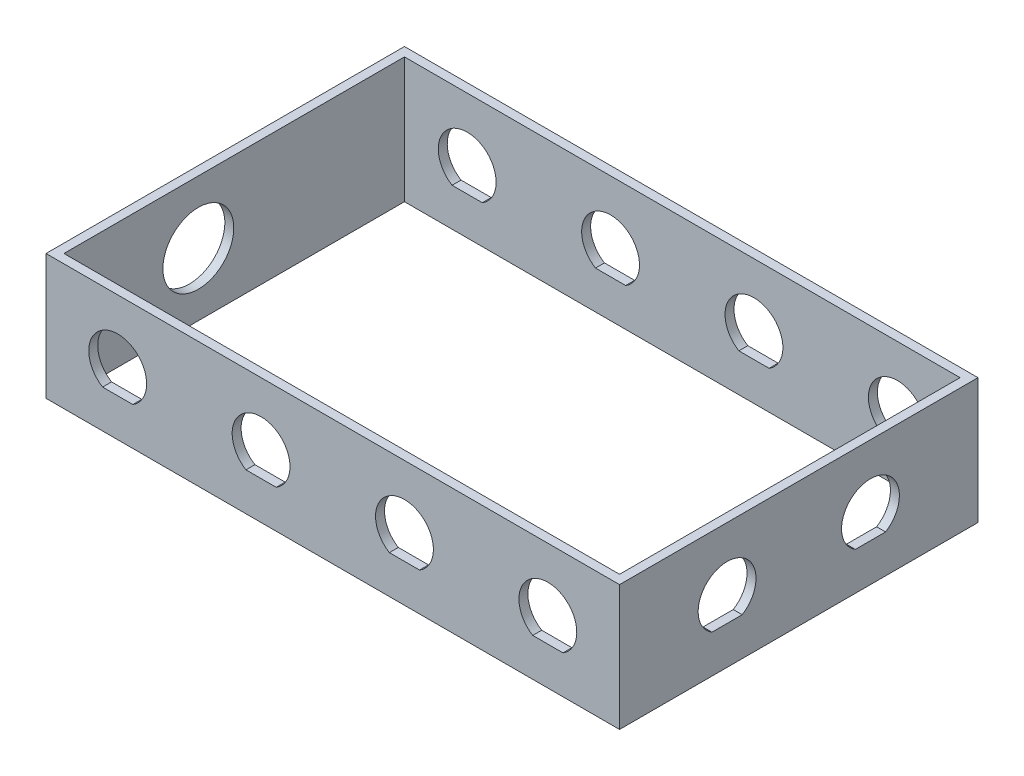
SolidWorks part; units mm, degrees
material "1060 Alloy"
ref_plane "Front Plane" through (0, 0, 0) normal (0, 0, 1) x (1, 0, 0)
ref_plane "Top Plane" through (0, 0, 0) normal (0, 1, 0) x (1, 0, 0)
ref_plane "Right Plane" through (0, 0, 0) normal (1, 0, 0) x (0, 0, -1)
sketch "Sketch1" plane through (0, 0, 0) normal (0, 1, 0) x (1, 0, 0)
  line L1 (101.6, -63.5) -> (-101.6, -63.5)
  line L2 (101.6, -63.5) -> (101.6, 63.5)
  line L3 (101.6, 63.5) -> (-101.6, 63.5)
  line L4 (-101.6, -63.5) -> (-101.6, 63.5)
  line L5 (101.6, -63.5) -> (-101.6, 63.5) construction
  line L6 (101.6, 63.5) -> (-101.6, -63.5) construction
  point P0 (0, 0)
  dimension "D1" = 127
  dimension "D2" = 203.2
extrude "Boss-Extrude1" add sketch "Sketch1" along normal blind 44.45
sketch "Sketch2" plane through (0, 44.45, 0) normal (0, 1, 0) x (1, 0, 0)
  line L8 (-98.425, 60.325) -> (-98.425, -60.325)
  line L9 (98.425, 60.325) -> (-98.425, 60.325)
  line L10 (98.425, -60.325) -> (98.425, 60.325)
  line L11 (-98.425, -60.325) -> (98.425, -60.325)
  line L12 (-98.425, 60.325) -> (-98.425, -60.325)
  line L13 (98.425, 60.325) -> (-98.425, 60.325)
  line L14 (98.425, -60.325) -> (98.425, 60.325)
  line L15 (-98.425, -60.325) -> (98.425, -60.325)
  dimension "D1" = 3.175
extrude "Cut-Extrude1" cut sketch "Sketch2" against normal through all
sketch "Sketch4" plane through (0, 44.45, 0) normal (0, 1, 0) x (1, 0, 0)
  line L4 (101.6, 63.5) -> (-101.6, 63.5)
  line L5 (-101.6, 63.5) -> (-101.6, -63.5)
  line L6 (-101.6, -63.5) -> (101.6, -63.5)
  line L7 (101.6, -63.5) -> (101.6, 63.5)
  line L9 (-98.425, -60.325) -> (98.425, -60.325)
  line L10 (-98.425, -60.325) -> (-98.425, 60.325)
  line L11 (-98.425, 60.325) -> (98.425, 60.325)
  line L12 (98.425, -60.325) -> (98.425, 60.325)
  line L13 (-98.425, -60.325) -> (98.425, 60.325) construction
  line L14 (-98.425, 60.325) -> (98.425, -60.325) construction
  point P12 (0, 0)
  dimension "D1" = 3.175
  dimension "D2" = 3.175
  dimension "D3" = 3.175
  dimension "D4" = 3.175
extrude "Boss-Extrude2" add sketch "Sketch4" against normal blind 6.35
sketch "Sketch10" plane through (0, 0, 63.5) normal (0, 0, 1) x (1, 0, 0)
  line L0 (0, 22.225) -> (50.8, 22.225) construction
  line L1 (-101.6, 0) -> (101.6, 0) construction
  line L3 (-104.775, 13.4874) -> (104.775, 13.4874)
  line L6 (50.8, 22.225) -> (101.6, 22.225) construction
  line L7 (101.6, 44.45) -> (101.6, 0) construction
  line L8 (0, 22.225) -> (-50.8, 22.225) construction
  line L9 (-50.8, 22.225) -> (-101.6, 22.225) construction
  line L10 (-101.6, 44.45) -> (-101.6, 0) construction
  circle A0 centre (-76.2, 22.225) radius 10.2489
  circle A1 centre (-25.4, 22.225) radius 10.2489
  circle A2 centre (25.4, 22.225) radius 10.2489
  circle A3 centre (76.2, 22.225) radius 10.2489
  point P5 (-76.2, 22.225)
  point P9 (-25.4, 22.225)
  point P12 (25.4, 22.225)
  point P13 (76.2, 22.225)
  dimension "D2" = 22.225
  dimension "D1" = 20.4978
  dimension "D3" = 8.7376
extrude "Cut-Extrude5" cut sketch "Sketch10" against normal through all
sketch "Sketch12" plane through (101.6, 0, 0) normal (1, 0, 0) x (0, 0, -1)
  line L0 (63.5, 22.225) -> (-63.5, 22.225) construction
  line L1 (63.5, 44.45) -> (63.5, 0) construction
  line L2 (-63.5, 44.45) -> (-63.5, 0) construction
  line L4 (-63.5, 13.4874) -> (63.5, 13.4874)
  circle A0 centre (-25.4, 22.225) radius 10.2489
  circle A1 centre (25.4, 22.225) radius 10.2489
  point P6 (63.5, 22.225)
  point P7 (-25.4, 22.225)
  point P10 (25.4, 22.225)
  dimension "D2" = 8.7376
  dimension "D3" = 20.4978
  dimension "D1" = 38.1
  dimension "D4" = 38.1
extrude "Cut-Extrude6" cut sketch "Sketch12" against normal up to next
sketch "Sketch13" plane through (-101.6, 0, 0) normal (-1, 0, 0) x (0, 0, 1)
  line L0 (63.5, 22.225) -> (-63.5, 22.225) construction
  line L1 (63.5, 44.45) -> (63.5, 0) construction
  line L2 (-63.5, 44.45) -> (-63.5, 0) construction
  line L4 (-63.5, 44.45) -> (63.5, 44.45) construction
  circle A0 centre (12.7, 22.225) radius 12.554
  point P6 (25.4, 22.225)
  point P7 (12.7, 22.225)
  dimension "D3" = 25.1079
  dimension "D4" = 22.225
  dimension "D1" = 38.1
  dimension "D2" = 76.2
extrude "Cut-Extrude7" cut sketch "Sketch13" against normal up to next
